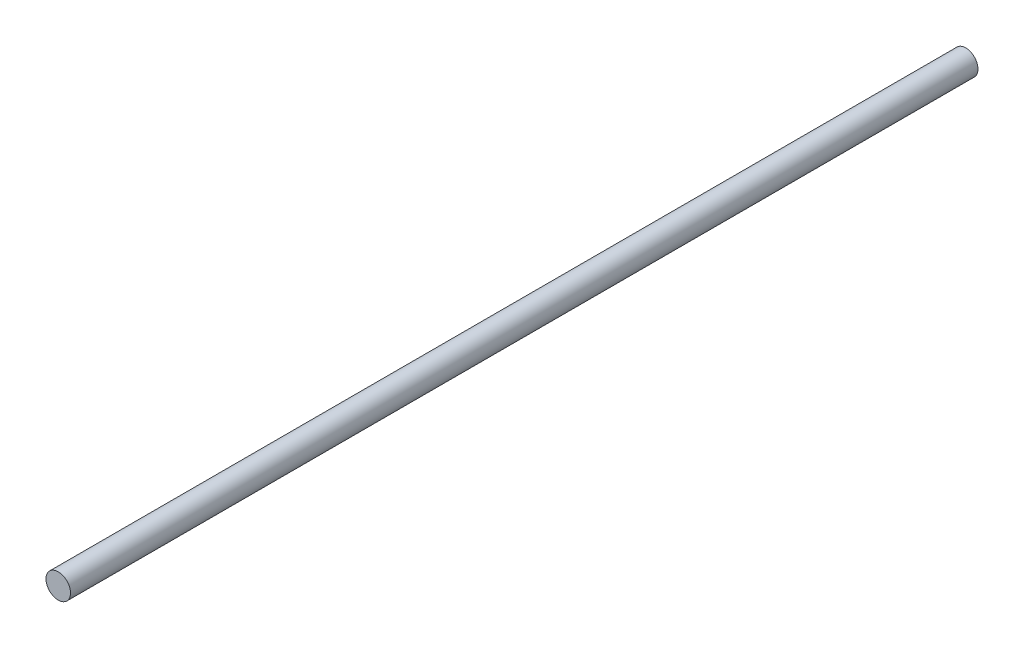
SolidWorks part; units mm, degrees
ref_plane "Front Plane" through (0, 0, 0) normal (0, 0, 1) x (1, 0, 0)
ref_plane "Top Plane" through (0, 0, 0) normal (0, 1, 0) x (1, 0, 0)
ref_plane "Right Plane" through (0, 0, 0) normal (1, 0, 0) x (0, 0, -1)
sketch "Sketch1" plane through (0, 0, 0) normal (0, 0, 1) x (1, 0, 0)
  circle A0 centre (0, 0) radius 2.0612
  dimension "D1" = 4.1224
extrude "Boss-Extrude1" add sketch "Sketch1" along normal blind 152.4
